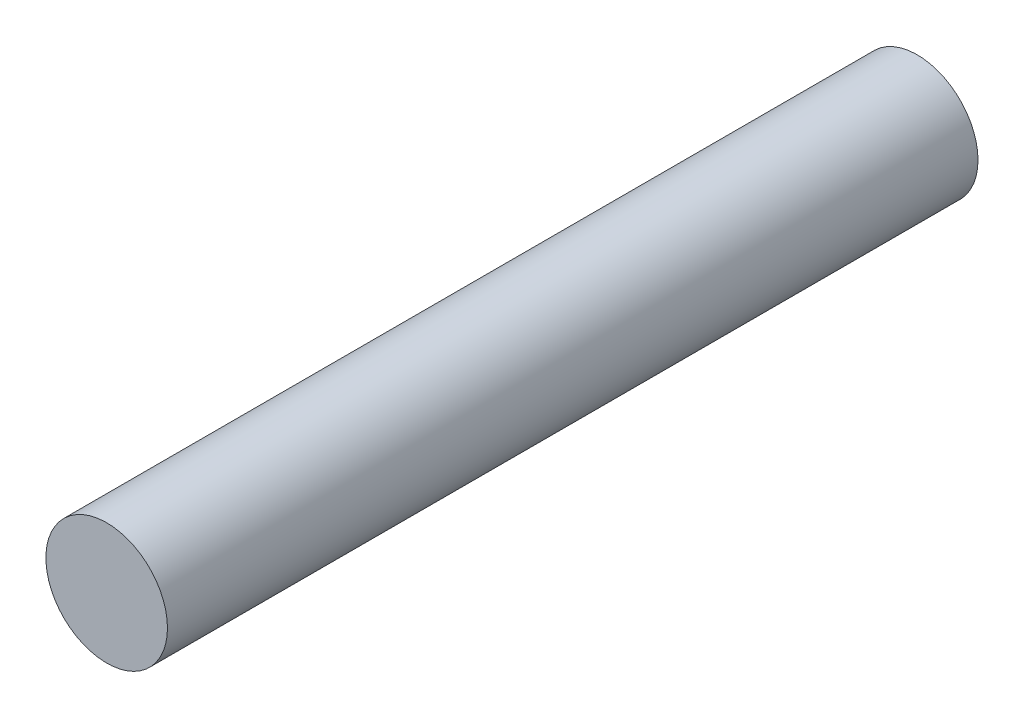
SolidWorks part; units mm, degrees
material "Brass"
ref_plane "Front Plane" through (0, 0, 0) normal (0, 0, 1) x (1, 0, 0)
ref_plane "Top Plane" through (0, 0, 0) normal (0, 1, 0) x (1, 0, 0)
ref_plane "Right Plane" through (0, 0, 0) normal (1, 0, 0) x (0, 0, -1)
sketch "Sketch1" plane through (0, 0, 0) normal (0, 0, 1) x (1, 0, 0)
  circle A0 centre (0, 0) radius 1.5
extrude "Boss-Extrude1" add sketch "Sketch1" along normal blind 20
